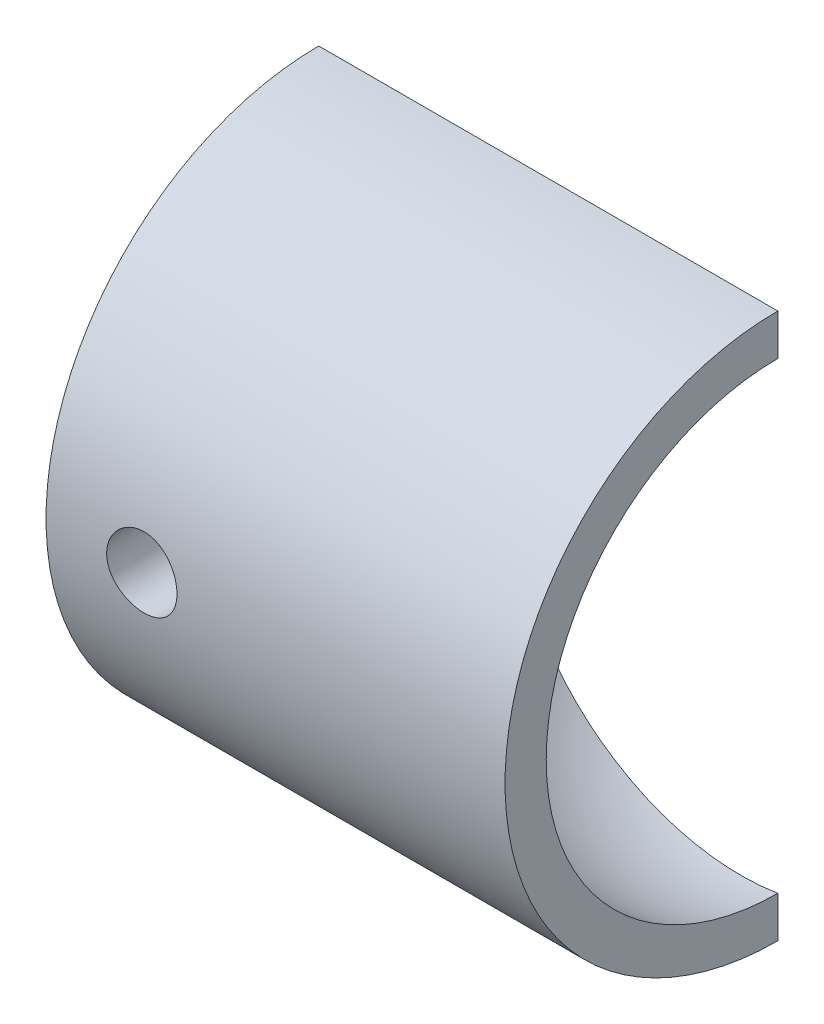
SolidWorks part; units mm, degrees
ref_plane "Alzado" through (0, 0, 0) normal (0, 0, 1) x (1, 0, 0)
ref_plane "Planta" through (0, 0, 0) normal (0, 1, 0) x (1, 0, 0)
ref_plane "Vista lateral" through (0, 0, 0) normal (1, 0, 0) x (0, 0, -1)
sketch "Croquis1" plane through (0, 0, 0) normal (0, 1, 0) x (1, 0, 0)
  line L0 (-10, 0) -> (-18, 0)
  line L1 (1.5747, 11.6308) -> (-18, 11.6308)
  line L4 (-18, 11.6308) -> (-18, 0)
  line L7 (1.5747, 9.8752) -> (1.5747, 11.6308)
  arc A0 (1.5747, 9.8752) -> (-10, 0) centre (0, 0) ccw
  dimension "D1" = 10
  dimension "D2" = 8
revolve "Revolución1" add sketch "Croquis1" angle 360 about L0
sketch "Croquis3" plane through (1.5747, 0, 0) normal (1, 0, 0) x (0, 0, -1)
  line L1 (0, 0) -> (0, -16.5867)
  line L2 (0, 0) -> (0, 15.9173)
  line L3 (0, -16.5867) -> (12.9851, -16.5867)
  line L4 (12.9851, -16.5867) -> (12.9851, 15.9173)
  line L5 (12.9851, 15.9173) -> (0, 15.9173)
extrude "Cortar-Extruir1" cut sketch "Croquis3" against normal blind 50
sketch "Croquis4" plane through (0, 0, 0) normal (0, 0, -1) x (-1, 0, 0)
  circle A0 centre (13.917, 0) radius 1.5
extrude "Cortar-Extruir2" cut sketch "Croquis4" against normal blind 20
